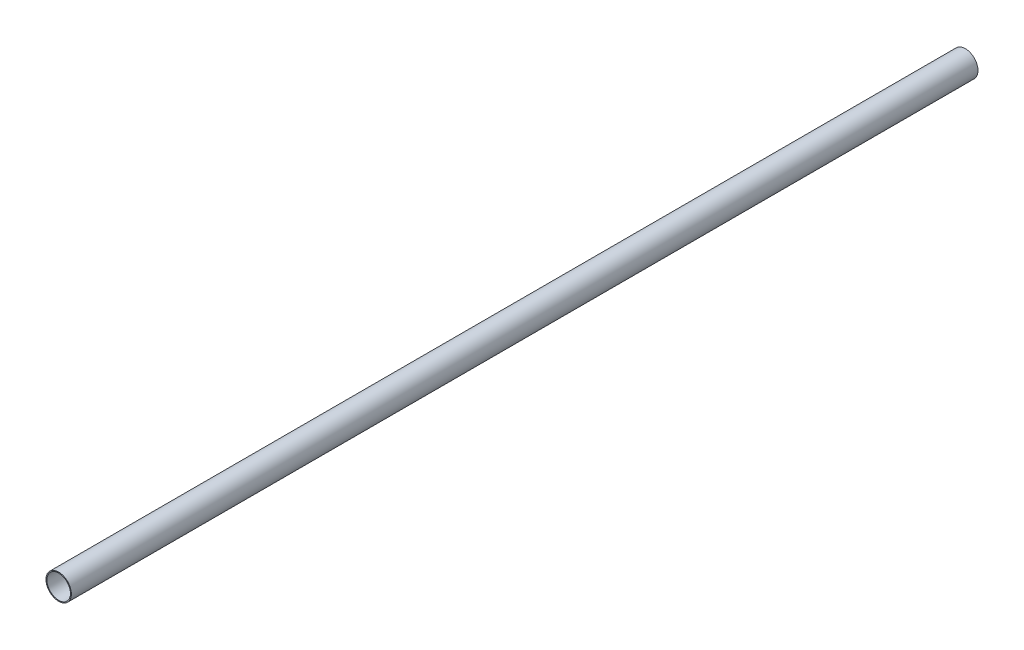
SolidWorks part; units mm, degrees
ref_plane "Front Plane" through (0, 0, 0) normal (0, 0, 1) x (1, 0, 0)
ref_plane "Top Plane" through (0, 0, 0) normal (0, 1, 0) x (1, 0, 0)
ref_plane "Right Plane" through (0, 0, 0) normal (1, 0, 0) x (0, 0, -1)
sketch "Sketch1" plane through (0, 0, 0) normal (0, 0, 1) x (1, 0, 0)
  circle A0 centre (0, 0) radius 14
  circle A1 centre (0, 0) radius 13
  dimension "D1" = 28
  dimension "D2" = 26
extrude "Boss-Extrude1" add sketch "Sketch1" against normal blind 1000
